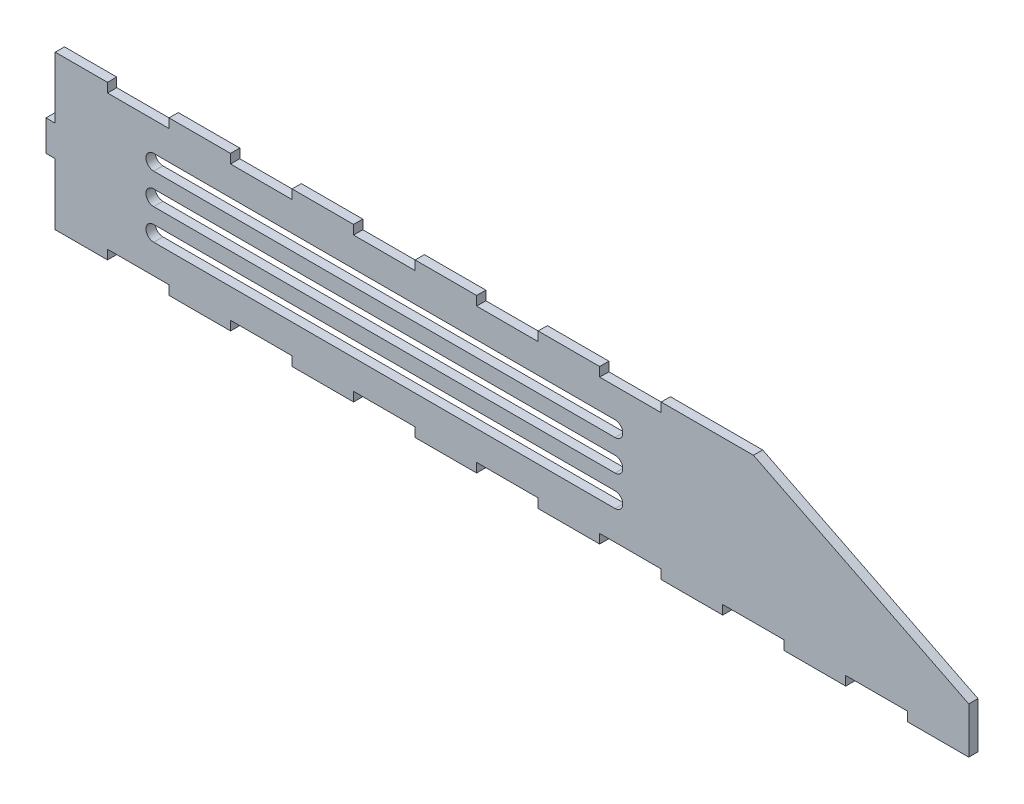
SolidWorks part; units mm, degrees
ref_plane "Front Plane" through (0, 0, 0) normal (0, 0, 1) x (1, 0, 0)
ref_plane "Top Plane" through (0, 0, 0) normal (0, 1, 0) x (1, 0, 0)
ref_plane "Right Plane" through (0, 0, 0) normal (1, 0, 0) x (0, 0, -1)
sketch "Sketch1" plane through (0, 0, 0) normal (0, 0, 1) x (1, 0, 0)
  line L0 (80, 25) -> (150, -10)
  line L1 (150, -25) -> (-150, -25)
  line L2 (150, -25) -> (150, -10)
  line L3 (80, 25) -> (-150, 25)
  line L4 (-150, -25) -> (-150, 25)
  point P0 (0, 0)
extrude "Boss-Extrude1" add sketch "Sketch1" along normal blind 3
sketch "Sketch2" plane through (0, 0, 3) normal (0, 0, 1) x (1, 0, 0)
  line L0 (-110, 25) -> (-130, 25)
  line L1 (-110, 22) -> (-130, 22)
  line L2 (-70, 25) -> (-90, 25)
  line L3 (-70, 22) -> (-90, 22)
  line L4 (-30, 25) -> (-50, 25)
  line L5 (-150, 25) -> (-150, -25)
  line L6 (-150, -25) -> (150, -25)
  line L7 (150, -25) -> (150, -10)
  line L8 (150, -10) -> (80, 25)
  line L9 (80, 25) -> (-150, 25)
  line L10 (-150, 15) -> (-150, 5)
  line L11 (-130, -25) -> (-110, -25)
  line L15 (-130, 25) -> (-130, 22)
  line L16 (-110, 25) -> (-110, 22)
  line L17 (-90, 25) -> (-90, 22)
  line L18 (-70, 25) -> (-70, 22)
  line L19 (-50, 25) -> (-50, 22)
  line L20 (-147, 22) -> (-147, -22)
  line L21 (-147, -22) -> (147, -22)
  line L22 (147, -22) -> (147, -11.8541)
  line L23 (147, -11.8541) -> (79.2918, 22)
  line L24 (79.2918, 22) -> (-147, 22)
  line L25 (-147, 15) -> (-147, 5)
  line L26 (-130, -22) -> (-110, -22)
  line L30 (-30, 25) -> (-30, 22)
  line L31 (-10, 25) -> (-10, 22)
  line L32 (10, 25) -> (10, 22)
  line L33 (30, 25) -> (30, 22)
  line L34 (50, 25) -> (50, 22)
  line L39 (-130, -22) -> (-130, -25)
  line L40 (-110, -22) -> (-110, -25)
  line L41 (-90, -22) -> (-90, -25)
  line L42 (-70, -22) -> (-70, -25)
  line L43 (-50, -22) -> (-50, -25)
  line L44 (-30, -22) -> (-30, -25)
  line L45 (-10, -22) -> (-10, -25)
  line L46 (10, -22) -> (10, -25)
  line L47 (30, -22) -> (30, -25)
  line L48 (50, -22) -> (50, -25)
  line L49 (70, -22) -> (70, -25)
  line L50 (90, -22) -> (90, -25)
  line L51 (110, -22) -> (110, -25)
  line L52 (130, -22) -> (130, -25)
  line L53 (-147, 15) -> (-150, 15)
  line L54 (-147, 5) -> (-150, 5)
  line L55 (-147, -5) -> (-150, -5)
  line L56 (-147, -15) -> (-150, -15)
  line L57 (-90, -22) -> (-70, -22)
  line L58 (-90, -25) -> (-70, -25)
  line L59 (-50, -22) -> (-30, -22)
  line L60 (-50, -25) -> (-30, -25)
  line L61 (-10, -22) -> (10, -22)
  line L62 (-10, -25) -> (10, -25)
  line L63 (30, -22) -> (50, -22)
  line L64 (30, -25) -> (50, -25)
  line L65 (70, -22) -> (90, -22)
  line L66 (70, -25) -> (90, -25)
  line L67 (110, -22) -> (130, -22)
  line L68 (110, -25) -> (130, -25)
  line L69 (-30, 22) -> (-50, 22)
  line L70 (10, 25) -> (-10, 25)
  line L71 (10, 22) -> (-10, 22)
  line L72 (50, 25) -> (30, 25)
  line L73 (50, 22) -> (30, 22)
  line L74 (-150, -5) -> (-150, -15)
  line L75 (-147, -5) -> (-147, -15)
  line L76 (110, 25) -> (110, 6.6459) [skipped]
  line L77 (70, 25) -> (70, 22) [skipped]
  line L78 (90, 20) -> (90, 16.6459) [skipped]
  line L79 (130, 0) -> (130, -3.3541) [skipped]
  dimension "D1" = 0
  dimension "D2" = 3
extrude "Cut-Extrude1" cut sketch "Sketch2" against normal blind 3
sketch "Sketch3" plane through (0, 0, 3) normal (0, 0, 1) x (1, 0, 0)
  line L1 (-147, 15) -> (-150, 15)
  line L2 (-147, 15) -> (-147, 25)
  line L3 (-147, 25) -> (-150, 25)
  line L4 (-150, 15) -> (-150, 25)
  line L5 (-150, -25) -> (-147, -25)
  line L6 (-150, -25) -> (-150, -15)
  line L7 (-150, -15) -> (-147, -15)
  line L8 (-147, -25) -> (-147, -15)
extrude "Cut-Extrude2" cut sketch "Sketch3" against normal blind 3
sketch "Sketch4" plane through (0, 0, 3) normal (0, 0, 1) x (1, 0, 0)
  line L7 (35, 10) -> (-115, 10) construction
  line L8 (35, 7.5) -> (-115, 7.5)
  line L9 (35, 12.5) -> (-115, 12.5)
  line L10 (35, 0) -> (-115, 0) construction
  line L11 (35, -2.5) -> (-115, -2.5)
  line L12 (35, 2.5) -> (-115, 2.5)
  line L13 (35, -10) -> (-115, -10) construction
  line L14 (35, -12.5) -> (-115, -12.5)
  line L15 (35, -7.5) -> (-115, -7.5)
  arc A0 (35, 7.5) -> (35, 12.5) centre (35, 10) ccw
  arc A1 (-115, 12.5) -> (-115, 7.5) centre (-115, 10) ccw
  arc A2 (35, -2.5) -> (35, 2.5) centre (35, 0) ccw
  arc A3 (-115, 2.5) -> (-115, -2.5) centre (-115, 0) ccw
  arc A4 (35, -12.5) -> (35, -7.5) centre (35, -10) ccw
  arc A5 (-115, -7.5) -> (-115, -12.5) centre (-115, -10) ccw
  point P14 (-40, 10)
  point P20 (-40, 0)
  point P27 (-40, -10)
extrude "Cut-Extrude3" cut sketch "Sketch4" against normal blind 3
